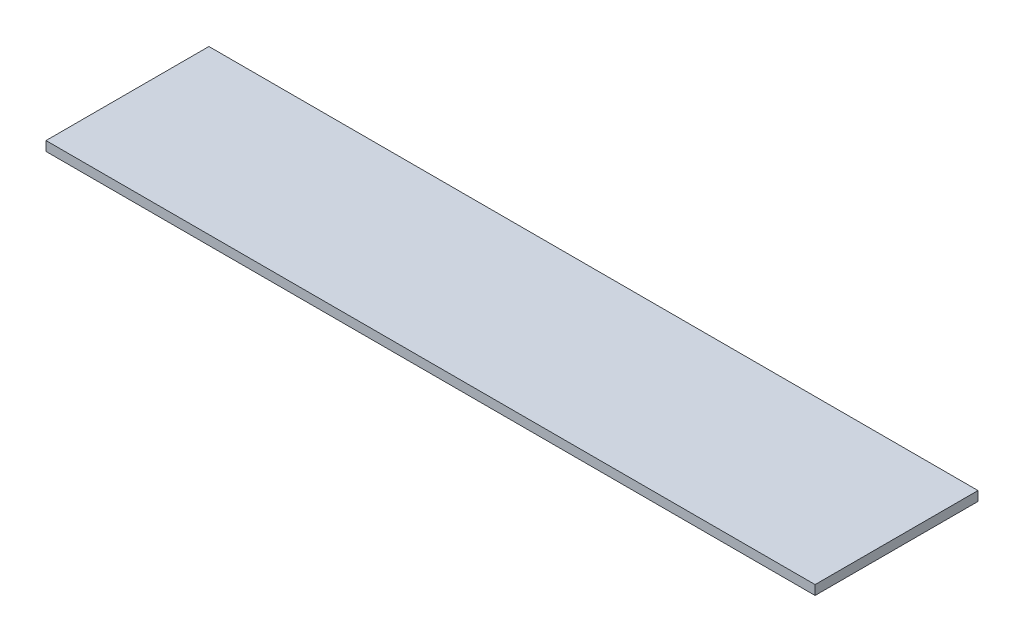
SolidWorks part; units mm, degrees
ref_plane "Front Plane" through (0, 0, 0) normal (0, 0, 1) x (1, 0, 0)
ref_plane "Top Plane" through (0, 0, 0) normal (0, 1, 0) x (1, 0, 0)
ref_plane "Right Plane" through (0, 0, 0) normal (1, 0, 0) x (0, 0, -1)
sketch "Sketch1" plane through (0, 0, 0) normal (0, 1, 0) x (1, 0, 0)
  line L1 (-203, -43) -> (203, -43)
  line L2 (-203, -43) -> (-203, 43)
  line L3 (-203, 43) -> (203, 43)
  line L4 (203, -43) -> (203, 43)
  line L5 (-203, -43) -> (203, 43) construction
  line L6 (-203, 43) -> (203, -43) construction
  point P0 (0, 0)
  dimension "D1" = 406
  dimension "D2" = 86
extrude "Boss-Extrude1" add sketch "Sketch1" along normal blind 5
